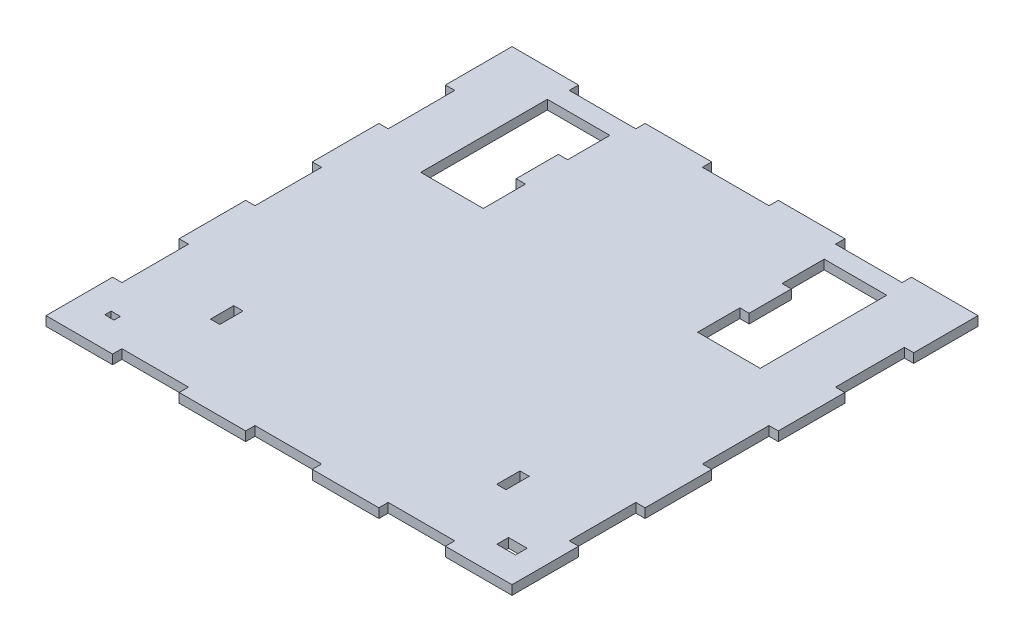
SolidWorks part; units mm, degrees
ref_plane "Front Plane" through (0, 0, 0) normal (0, 0, 1) x (1, 0, 0)
ref_plane "Top Plane" through (0, 0, 0) normal (0, 1, 0) x (1, 0, 0)
ref_plane "Right Plane" through (0, 0, 0) normal (1, 0, 0) x (0, 0, -1)
sketch "Sketch1" plane through (0, 0, 0) normal (0, 1, 0) x (1, 0, 0)
  line L1 (0, 0) -> (-254, 0)
  line L2 (0, 0) -> (0, 254)
  line L3 (0, 254) -> (-254, 254)
  line L4 (-254, 0) -> (-254, 254)
  dimension "D1" = 254
  dimension "D2" = 254
extrude "Boss-Extrude1" add sketch "Sketch1" along normal blind 5.08
sketch "Sketch2" plane through (0, 0, 0) normal (0, 0, 1) x (1, 0, 0)
  line L0 (-254, 0) -> (-217.7143, 0) construction
  line L1 (-254, 0) -> (0, 0) construction
  line L2 (-217.7143, 0) -> (-181.4286, 0) construction
  line L3 (-181.4286, 0) -> (-145.1429, 0) construction
  line L4 (-145.1429, 0) -> (-108.8571, 0) construction
  line L5 (-108.8571, 0) -> (-72.5714, 0) construction
  line L6 (-72.5714, 0) -> (-36.2857, 0) construction
  line L7 (-36.2857, 0) -> (0, 0) construction
  line L8 (-254, 5.08) -> (0, 5.08) construction
  line L9 (-217.7143, 0) -> (-181.4286, 0)
  line L10 (-217.7143, 0) -> (-217.7143, 5.08)
  line L11 (-217.7143, 5.08) -> (-181.4286, 5.08)
  line L12 (-181.4286, 0) -> (-181.4286, 5.08)
  line L14 (-145.1429, 0) -> (-108.8571, 0)
  line L15 (-145.1429, 0) -> (-145.1429, 5.08)
  line L16 (-145.1429, 5.08) -> (-108.8571, 5.08)
  line L17 (-108.8571, 0) -> (-108.8571, 5.08)
  line L18 (-72.5714, 0) -> (-36.2857, 0)
  line L19 (-72.5714, 0) -> (-72.5714, 5.08)
  line L20 (-72.5714, 5.08) -> (-36.2857, 5.08)
  line L21 (-36.2857, 0) -> (-36.2857, 5.08)
extrude "Cut-Extrude1" cut sketch "Sketch2" against normal blind 5.08
sketch "Sketch3" plane through (0, 0, 0) normal (1, 0, 0) x (0, 0, -1)
  line L0 (0, 0) -> (36.2857, 0) construction
  line L1 (0, 0) -> (254, 0) construction
  line L2 (36.2857, 0) -> (72.5714, 0) construction
  line L3 (72.5714, 0) -> (108.8571, 0) construction
  line L4 (108.8571, 0) -> (145.1429, 0) construction
  line L5 (145.1429, 0) -> (181.4286, 0) construction
  line L6 (181.4286, 0) -> (217.7143, 0) construction
  line L7 (217.7143, 0) -> (254, 0) construction
  line L8 (0, 5.08) -> (254, 5.08) construction
  line L9 (36.2857, 0) -> (72.5714, 0)
  line L10 (36.2857, 0) -> (36.2857, 5.08)
  line L11 (36.2857, 5.08) -> (72.5714, 5.08)
  line L12 (72.5714, 0) -> (72.5714, 5.08)
  line L14 (108.8571, 0) -> (145.1429, 0)
  line L15 (108.8571, 0) -> (108.8571, 5.08)
  line L16 (108.8571, 5.08) -> (145.1429, 5.08)
  line L17 (145.1429, 0) -> (145.1429, 5.08)
  line L18 (181.4286, 0) -> (218.9529, 0)
  line L19 (181.4286, 0) -> (181.4286, 5.08)
  line L20 (181.4286, 5.08) -> (218.9529, 5.08)
  line L21 (218.9529, 0) -> (218.9529, 5.08)
extrude "Cut-Extrude2" cut sketch "Sketch3" against normal blind 5.08
sketch "Sketch4" plane through (0, 0, -254) normal (0, 0, -1) x (-1, 0, 0)
  line L0 (0, 0) -> (36.2857, 0) construction
  line L1 (0, 0) -> (254, 0) construction
  line L2 (36.2857, 0) -> (72.5714, 0) construction
  line L3 (72.5714, 0) -> (108.8571, 0) construction
  line L4 (108.8571, 0) -> (145.1429, 0) construction
  line L5 (145.1429, 0) -> (181.4286, 0) construction
  line L6 (181.4286, 0) -> (217.7143, 0) construction
  line L7 (217.7143, 0) -> (254, 0) construction
  line L8 (0, 5.08) -> (254, 5.08) construction
  line L9 (36.2857, 0) -> (72.5714, 0)
  line L10 (36.2857, 0) -> (36.2857, 5.08)
  line L11 (36.2857, 5.08) -> (72.5714, 5.08)
  line L12 (72.5714, 0) -> (72.5714, 5.08)
  line L14 (108.8571, 0) -> (145.1429, 0)
  line L15 (108.8571, 0) -> (108.8571, 5.08)
  line L16 (108.8571, 5.08) -> (145.1429, 5.08)
  line L17 (145.1429, 0) -> (145.1429, 5.08)
  line L18 (181.4286, 0) -> (217.7143, 0)
  line L19 (181.4286, 0) -> (181.4286, 5.08)
  line L20 (181.4286, 5.08) -> (217.7143, 5.08)
  line L21 (217.7143, 0) -> (217.7143, 5.08)
extrude "Cut-Extrude3" cut sketch "Sketch4" against normal blind 5.08
sketch "Sketch5" plane through (-254, 0, 0) normal (-1, 0, 0) x (0, 0, 1)
  line L0 (-254, 0) -> (-217.7143, 0) construction
  line L1 (-254, 0) -> (0, 0) construction
  line L2 (-217.7143, 0) -> (-181.4286, 0) construction
  line L3 (-181.4286, 0) -> (-145.1429, 0) construction
  line L4 (-145.1429, 0) -> (-108.8571, 0) construction
  line L5 (-108.8571, 0) -> (-72.5714, 0) construction
  line L6 (-72.5714, 0) -> (-36.2857, 0) construction
  line L7 (-36.2857, 0) -> (0, 0) construction
  line L8 (-254, 5.08) -> (0, 5.08) construction
  line L9 (-217.7143, 0) -> (-181.4286, 0)
  line L10 (-217.7143, 0) -> (-217.7143, 5.08)
  line L11 (-217.7143, 5.08) -> (-181.4286, 5.08)
  line L12 (-181.4286, 0) -> (-181.4286, 5.08)
  line L14 (-145.1429, 0) -> (-108.8571, 0)
  line L15 (-145.1429, 0) -> (-145.1429, 5.08)
  line L16 (-145.1429, 5.08) -> (-108.8571, 5.08)
  line L17 (-108.8571, 0) -> (-108.8571, 5.08)
  line L18 (-72.5714, 0) -> (-36.2857, 0)
  line L19 (-72.5714, 0) -> (-72.5714, 5.08)
  line L20 (-72.5714, 5.08) -> (-36.2857, 5.08)
  line L21 (-36.2857, 0) -> (-36.2857, 5.08)
extrude "Cut-Extrude4" cut sketch "Sketch5" against normal blind 5.08
sketch "Sketch6" plane through (0, 5.08, 0) normal (0, 1, 0) x (1, 0, 0)
  line L0 (-127, 248.92) -> (-127, 238.76) construction
  line L1 (-145.1429, 248.92) -> (-108.8571, 248.92) construction
  line L2 (-127, 238.76) -> (-63.5, 238.76) construction
  line L3 (-127, 238.76) -> (-190.5, 238.76)
  line L5 (-63.5, 238.76) -> (-34.5, 238.76)
  line L6 (-63.5, 238.76) -> (-63.5, 169.76)
  line L7 (-63.5, 169.76) -> (-34.5, 169.76)
  line L8 (-34.5, 238.76) -> (-34.5, 169.76)
  line L9 (-190.5, 238.76) -> (-219.5, 238.76)
  line L10 (-190.5, 238.76) -> (-190.5, 169.76)
  line L11 (-190.5, 169.76) -> (-219.5, 169.76)
  line L12 (-219.5, 238.76) -> (-219.5, 169.76)
  dimension "D1" = 10.16
  dimension "D2" = 63.5
  dimension "D3" = 29
  dimension "D4" = 69
  dimension "D5" = 29
  dimension "D6" = 69
extrude "Cut-Extrude5" cut sketch "Sketch6" against normal blind 5.08 contours L8 L5 L6 L7 | L9 L12 L11 L10
sketch "Sketch7" plane through (0, 5.08, 0) normal (0, 1, 0) x (1, 0, 0)
  line L0 (-49, 169.76) -> (-49, 43.18) construction
  line L1 (-63.5, 169.76) -> (-34.5, 169.76) construction
  line L2 (-49, 43.18) -> (-49, 5.08) construction
  line L3 (-36.2857, 5.08) -> (-72.5714, 5.08) construction
  line L4 (-49, 43.18) -> (-51.54, 43.18) construction
  line L5 (-49, 43.18) -> (-46.46, 43.18)
  line L7 (-46.46, 43.18) -> (-51.54, 43.18)
  line L8 (-46.46, 43.18) -> (-46.46, 55.88)
  line L9 (-46.46, 55.88) -> (-51.54, 55.88)
  line L10 (-51.54, 43.18) -> (-51.54, 55.88)
  dimension "D1" = 38.1
  dimension "D2" = 2.54
  dimension "D3" = 12.7
extrude "Cut-Extrude6" cut sketch "Sketch7" against normal blind 5.08 contours L10 L7 L5 L8 L9
sketch "Sketch8" plane through (0, 5.08, 0) normal (0, 1, 0) x (1, 0, 0)
  line L0 (-205, 169.76) -> (-205, 43.18) construction
  line L1 (-190.5, 169.76) -> (-219.5, 169.76) construction
  line L2 (-205, 43.18) -> (-205, 5.08) construction
  line L3 (-181.4286, 5.08) -> (-217.7143, 5.08) construction
  line L4 (-205, 43.18) -> (-202.46, 43.18) construction
  line L5 (-205, 43.18) -> (-207.54, 43.18) construction
  line L7 (-202.46, 43.18) -> (-207.54, 43.18)
  line L8 (-202.46, 43.18) -> (-202.46, 55.88)
  line L9 (-202.46, 55.88) -> (-207.54, 55.88)
  line L10 (-207.54, 43.18) -> (-207.54, 55.88)
  dimension "D1" = 38.1
  dimension "D2" = 2.54
  dimension "D3" = 12.7
extrude "Cut-Extrude7" cut sketch "Sketch8" against normal blind 5.08
sketch "Sketch9" plane through (-63.5, 0, 0) normal (1, 0, 0) x (0, 0, -1)
  line L0 (169.76, 5.08) -> (192.76, 5.08)
  line L1 (238.76, 5.08) -> (169.76, 5.08) construction
  line L2 (192.76, 5.08) -> (215.76, 5.08)
  line L3 (215.76, 5.08) -> (238.76, 5.08)
  line L4 (238.76, 0) -> (169.76, 0) construction
  line L5 (169.76, 5.08) -> (192.76, 5.08)
  line L6 (169.76, 5.08) -> (169.76, 0)
  line L7 (169.76, 0) -> (192.76, 0)
  line L8 (192.76, 5.08) -> (192.76, 0)
  line L10 (215.76, 5.08) -> (238.76, 5.08)
  line L11 (215.76, 5.08) -> (215.76, 0)
  line L12 (215.76, 0) -> (238.76, 0)
  line L13 (238.76, 5.08) -> (238.76, 0)
  line M4 (238.76, 5.08) -> (169.76, 5.08)
  line M5 (169.76, 5.08) -> (169.76, 0)
  line M6 (169.76, 0) -> (238.76, 0)
  line M7 (238.76, 0) -> (238.76, 5.08)
extrude "Cut-Extrude8" cut sketch "Sketch9" against normal blind 5.08 contours L8 M4 M5 M6 | L11 M4 M6 M7
sketch "Sketch10" plane through (-190.5, 0, 0) normal (-1, 0, 0) x (0, 0, 1)
  line L0 (-238.76, 5.08) -> (-215.76, 5.08) construction
  line L1 (-238.76, 5.08) -> (-169.76, 5.08) construction
  line L2 (-215.76, 5.08) -> (-192.76, 5.08) construction
  line L3 (-192.76, 5.08) -> (-169.76, 5.08) construction
  line L4 (-238.76, 0) -> (-169.76, 0) construction
  line L5 (-169.76, 5.08) -> (-192.76, 5.08)
  line L6 (-169.76, 5.08) -> (-169.76, 0)
  line L7 (-169.76, 0) -> (-192.76, 0)
  line L8 (-192.76, 5.08) -> (-192.76, 0)
  line L10 (-215.76, 5.08) -> (-238.76, 5.08)
  line L11 (-215.76, 5.08) -> (-215.76, 0)
  line L12 (-215.76, 0) -> (-238.76, 0)
  line L13 (-238.76, 5.08) -> (-238.76, 0)
extrude "Cut-Extrude9" cut sketch "Sketch10" against normal blind 5.08
sketch "Sketch11" plane through (0, 5.08, 0) normal (0, 1, 0) x (1, 0, 0)
  line L2 (-13.0629, 14.9679) -> (-23.2229, 14.9679)
  line L4 (-18.1429, 18.1429) -> (-13.0629, 18.1429) construction
  line L5 (-18.1429, 18.1429) -> (-23.2229, 18.1429) construction
  line L6 (-18.1429, 18.1429) -> (-18.1429, 21.3179) construction
  line L7 (-18.1429, 18.1429) -> (-18.1429, 14.9679) construction
  line L8 (-13.0629, 14.9679) -> (-13.0629, 21.3179)
  line L9 (-13.0629, 21.3179) -> (-23.2229, 21.3179)
  line L10 (-23.2229, 14.9679) -> (-23.2229, 21.3179)
  dimension "D1" = 5.08
  dimension "D2" = 3.175
extrude "Cut-Extrude10" cut sketch "Sketch11" against normal blind 5.08
sketch "Sketch12" plane through (0, 5.08, 0) normal (0, 1, 0) x (1, 0, 0)
  line L2 (-233.3592, 16.3981) -> (-238.3551, 16.3981)
  line L4 (-235.8571, 18.1429) -> (-238.3551, 18.1429) construction
  line L5 (-235.8571, 18.1429) -> (-233.3592, 18.1429) construction
  line L6 (-235.8571, 18.1429) -> (-235.8571, 16.3981) construction
  line L7 (-235.8571, 18.1429) -> (-235.8571, 19.8876) construction
  line L8 (-233.3592, 16.3981) -> (-233.3592, 19.8876)
  line L9 (-233.3592, 19.8876) -> (-238.3551, 19.8876)
  line L10 (-238.3551, 16.3981) -> (-238.3551, 19.8876)
extrude "Cut-Extrude11" cut sketch "Sketch12" against normal blind 5.08
equation "\"MDFThickness\"= .2in"
equation "\"D1@Boss-Extrude1\"=\"MDFThickness\""
equation "\"D1@Cut-Extrude1\"=\"MDFThickness\""
equation "\"D1@Cut-Extrude2\"=\"MDFThickness\""
equation "\"D1@Cut-Extrude3\"=\"MDFThickness\""
equation "\"D1@Cut-Extrude4\"=\"MDFThickness\""
equation "\"D1@Sketch6\"=\"MDFThickness\" * 2"
equation "\"D1@Cut-Extrude5\"= \"MDFThickness\""
equation "\"D2@Sketch7\"=\"MDFThickness\" /2"
equation "\"D1@Cut-Extrude6\"=\"MDFThickness\""
equation "\"D2@Sketch8\"=\"MDFThickness\" / 2"
equation "\"D1@Cut-Extrude7\"=\"MDFThickness\""
equation "\"D1@Cut-Extrude8\"=\"MDFThickness\""
equation "\"D1@Cut-Extrude9\"=\"MDFThickness\""
equation "\"D1@Cut-Extrude10\"=\"MDFThickness\""
equation "\"D1@Cut-Extrude11\"=\"MDFThickness\""
